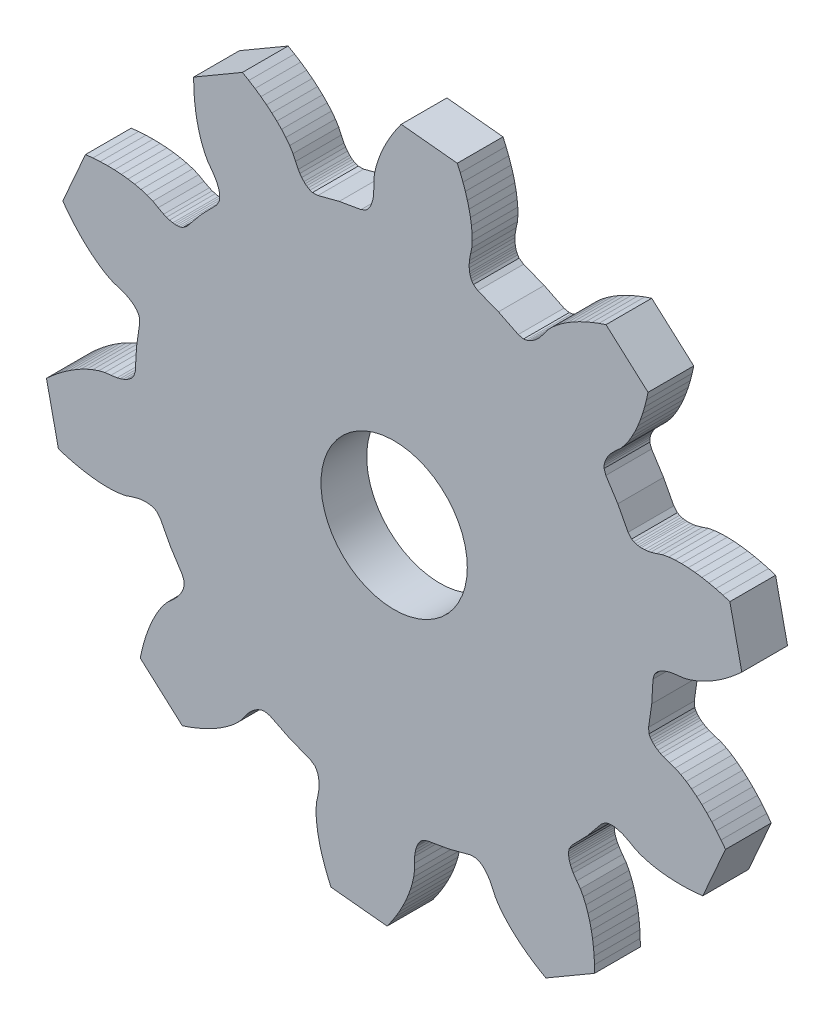
SolidWorks part; units mm, degrees
ref_plane "Front Plane" through (0, 0, 0) normal (0, 0, 1) x (1, 0, 0)
ref_plane "Top Plane" through (0, 0, 0) normal (0, 1, 0) x (1, 0, 0)
ref_plane "Right Plane" through (0, 0, 0) normal (1, 0, 0) x (0, 0, -1)
sketch "Sketch1" plane through (0, 0, 0) normal (0, 0, 1) x (1, 0, 0)
  line L0 (8.112, 16.6609) -> (7.8643, 16.9436)
  line L1 (7.8643, 16.9436) -> (7.7104, 17.0282)
  line L2 (7.7104, 17.0282) -> (7.5725, 17.0779)
  line L3 (7.5725, 17.0779) -> (7.4432, 17.1089)
  line L4 (7.4432, 17.1089) -> (7.3198, 17.1275)
  line L5 (7.3198, 17.1275) -> (7.2004, 17.1366)
  line L6 (7.2004, 17.1366) -> (6.971, 17.1338)
  line L7 (6.971, 17.1338) -> (6.7508, 17.1099)
  line L8 (6.7508, 17.1099) -> (6.5372, 17.0698)
  line L9 (6.5372, 17.0698) -> (6.1262, 16.9512)
  line L10 (6.1262, 16.9512) -> (5.7224, 16.8153)
  line L11 (5.7224, 16.8153) -> (5.2951, 16.7376)
  line L12 (5.2951, 16.7376) -> (4.8534, 16.6975)
  line L13 (4.8534, 16.6975) -> (4.4008, 16.6875)
  line L14 (4.4008, 16.6875) -> (3.9395, 16.7046)
  line L15 (3.9395, 16.7046) -> (3.4704, 16.7465)
  line L16 (3.4704, 16.7465) -> (2.9949, 16.812)
  line L17 (2.9949, 16.812) -> (2.5141, 16.9001)
  line L18 (2.5141, 16.9001) -> (2.0282, 17.0109)
  line L19 (2.0282, 17.0109) -> (1.5385, 17.1432)
  line L20 (1.5385, 17.1432) -> (1.0457, 17.2971)
  line L21 (1.0457, 17.2971) -> (0.2156, 21.1229)
  line L22 (0.2156, 21.1229) -> (0.6005, 21.4671)
  line L23 (0.6005, 21.4671) -> (0.9914, 21.7907)
  line L24 (0.9914, 21.7907) -> (1.3876, 22.0924)
  line L25 (1.3876, 22.0924) -> (1.7887, 22.3723)
  line L26 (1.7887, 22.3723) -> (2.1943, 22.6289)
  line L27 (2.1943, 22.6289) -> (2.6038, 22.8613)
  line L28 (2.6038, 22.8613) -> (3.0168, 23.068)
  line L29 (3.0168, 23.068) -> (3.4328, 23.2463)
  line L30 (3.4328, 23.2463) -> (3.8514, 23.3929)
  line L31 (3.8514, 23.3929) -> (4.2723, 23.4993)
  line L32 (4.2723, 23.4993) -> (4.6962, 23.543)
  line L33 (4.6962, 23.543) -> (5.1196, 23.6052)
  line L34 (5.1196, 23.6052) -> (5.3304, 23.6571)
  line L35 (5.3304, 23.6571) -> (5.5408, 23.7269)
  line L36 (5.5408, 23.7269) -> (5.7508, 23.8194)
  line L37 (5.7508, 23.8194) -> (5.8555, 23.8773)
  line L38 (5.8555, 23.8773) -> (5.9604, 23.9451)
  line L39 (5.9604, 23.9451) -> (6.065, 24.0269)
  line L40 (6.065, 24.0269) -> (6.1697, 24.1295)
  line L41 (6.1697, 24.1295) -> (6.2748, 24.2702)
  line L42 (6.2748, 24.2702) -> (6.383, 24.6301)
  line L43 (6.383, 24.6301) -> (6.4719, 26.1612)
  line L44 (6.4719, 26.1612) -> (6.6906, 27.6794)
  line L45 (6.6906, 27.6794) -> (6.6566, 28.0535)
  line L46 (6.6566, 28.0535) -> (6.5816, 28.2125)
  line L47 (6.5816, 28.2125) -> (6.4994, 28.334)
  line L48 (6.4994, 28.334) -> (6.4132, 28.435)
  line L49 (6.4132, 28.435) -> (6.3241, 28.5224)
  line L50 (6.3241, 28.5224) -> (6.2329, 28.5999)
  line L51 (6.2329, 28.5999) -> (6.0457, 28.7327)
  line L52 (6.0457, 28.7327) -> (5.8534, 28.843)
  line L53 (5.8534, 28.843) -> (5.6573, 28.9359)
  line L54 (5.6573, 28.9359) -> (5.255, 29.0815)
  line L55 (5.255, 29.0815) -> (4.8484, 29.209)
  line L56 (4.8484, 29.209) -> (4.4569, 29.3972)
  line L57 (4.4569, 29.3972) -> (4.0759, 29.6245)
  line L58 (4.0759, 29.6245) -> (3.7041, 29.8823)
  line L59 (3.7041, 29.8823) -> (3.3409, 30.1673)
  line L60 (3.3409, 30.1673) -> (2.986, 30.4767)
  line L61 (2.986, 30.4767) -> (2.6398, 30.8092)
  line L62 (2.6398, 30.8092) -> (2.3025, 31.1635)
  line L63 (2.3025, 31.1635) -> (1.9746, 31.5384)
  line L64 (1.9746, 31.5384) -> (1.6563, 31.9334)
  line L65 (1.6563, 31.9334) -> (1.348, 32.3477)
  line L66 (1.348, 32.3477) -> (2.9253, 35.9306)
  line L67 (2.9253, 35.9306) -> (3.4389, 35.9829)
  line L68 (3.4389, 35.9829) -> (3.9451, 36.0149)
  line L69 (3.9451, 36.0149) -> (4.4432, 36.0261)
  line L70 (4.4432, 36.0261) -> (4.9322, 36.0167)
  line L71 (4.9322, 36.0167) -> (5.4112, 35.986)
  line L72 (5.4112, 35.986) -> (5.8791, 35.9334)
  line L73 (5.8791, 35.9334) -> (6.3345, 35.8577)
  line L74 (6.3345, 35.8577) -> (6.776, 35.7576)
  line L75 (6.776, 35.7576) -> (7.2009, 35.6301)
  line L76 (7.2009, 35.6301) -> (7.604, 35.4688)
  line L77 (7.604, 35.4688) -> (7.9726, 35.2549)
  line L78 (7.9726, 35.2549) -> (8.3515, 35.0566)
  line L79 (8.3515, 35.0566) -> (8.5527, 34.9745)
  line L80 (8.5527, 34.9745) -> (8.7638, 34.9072)
  line L81 (8.7638, 34.9072) -> (8.988, 34.8587)
  line L82 (8.988, 34.8587) -> (9.1069, 34.844)
  line L83 (9.1069, 34.844) -> (9.2316, 34.8374)
  line L84 (9.2316, 34.8374) -> (9.3645, 34.8419)
  line L85 (9.3645, 34.8419) -> (9.5095, 34.8633)
  line L86 (9.5095, 34.8633) -> (9.6771, 34.9153)
  line L87 (9.6771, 34.9153) -> (9.9764, 35.1429)
  line L88 (9.9764, 35.1429) -> (10.9482, 36.3296)
  line L89 (10.9482, 36.3296) -> (12.0175, 37.4289)
  line L90 (12.0175, 37.4289) -> (12.2098, 37.7518)
  line L91 (12.2098, 37.7518) -> (12.2425, 37.9245)
  line L92 (12.2425, 37.9245) -> (12.2474, 38.071)
  line L93 (12.2474, 38.071) -> (12.237, 38.2034)
  line L94 (12.237, 38.2034) -> (12.2164, 38.3266)
  line L95 (12.2164, 38.3266) -> (12.1882, 38.4429)
  line L96 (12.1882, 38.4429) -> (12.1148, 38.6603)
  line L97 (12.1148, 38.6603) -> (12.0241, 38.8625)
  line L98 (12.0241, 38.8625) -> (11.92, 39.053)
  line L99 (11.92, 39.053) -> (11.6799, 39.4071)
  line L100 (11.6799, 39.4071) -> (11.4259, 39.7495)
  line L101 (11.4259, 39.7495) -> (11.2199, 40.1317)
  line L102 (11.2199, 40.1317) -> (11.0454, 40.5394)
  line L103 (11.0454, 40.5394) -> (10.8961, 40.9666)
  line L104 (10.8961, 40.9666) -> (10.7696, 41.4109)
  line L105 (10.7696, 41.4109) -> (10.6644, 41.8699)
  line L106 (10.6644, 41.8699) -> (10.5799, 42.3423)
  line L107 (10.5799, 42.3423) -> (10.5153, 42.8269)
  line L108 (10.5153, 42.8269) -> (10.4704, 43.3233)
  line L109 (10.4704, 43.3233) -> (10.445, 43.8297)
  line L110 (10.445, 43.8297) -> (10.4389, 44.3461)
  line L111 (10.4389, 44.3461) -> (13.8212, 46.3177)
  line L112 (13.8212, 46.3177) -> (14.2674, 46.0581)
  line L113 (14.2674, 46.0581) -> (14.6957, 45.7863)
  line L114 (14.6957, 45.7863) -> (15.1054, 45.5028)
  line L115 (15.1054, 45.5028) -> (15.4953, 45.2077)
  line L116 (15.4953, 45.2077) -> (15.8648, 44.9014)
  line L117 (15.8648, 44.9014) -> (16.2123, 44.5836)
  line L118 (16.2123, 44.5836) -> (16.5364, 44.2547)
  line L119 (16.5364, 44.2547) -> (16.8349, 43.9143)
  line L120 (16.8349, 43.9143) -> (17.1033, 43.5615)
  line L121 (17.1033, 43.5615) -> (17.3347, 43.194)
  line L122 (17.3347, 43.194) -> (17.5072, 42.8043)
  line L123 (17.5072, 42.8043) -> (17.6972, 42.421)
  line L124 (17.6972, 42.421) -> (17.8117, 42.2364)
  line L125 (17.8117, 42.2364) -> (17.9431, 42.0578)
  line L126 (17.9431, 42.0578) -> (18.096, 41.8869)
  line L127 (18.096, 41.8869) -> (18.1834, 41.8051)
  line L128 (18.1834, 41.8051) -> (18.2804, 41.7264)
  line L129 (18.2804, 41.7264) -> (18.3906, 41.6522)
  line L130 (18.3906, 41.6522) -> (18.5204, 41.5841)
  line L131 (18.5204, 41.5841) -> (18.6868, 41.5275)
  line L132 (18.6868, 41.5275) -> (19.0624, 41.5359)
  line L133 (19.0624, 41.5359) -> (20.5461, 41.9247)
  line L134 (20.5461, 41.9247) -> (22.0576, 42.1856)
  line L135 (22.0576, 42.1856) -> (22.4031, 42.3337)
  line L136 (22.4031, 42.3337) -> (22.5308, 42.4541)
  line L137 (22.5308, 42.4541) -> (22.621, 42.5699)
  line L138 (22.621, 42.5699) -> (22.6903, 42.6832)
  line L139 (22.6903, 42.6832) -> (22.7462, 42.7949)
  line L140 (22.7462, 42.7949) -> (22.7917, 42.9054)
  line L141 (22.7917, 42.9054) -> (22.86, 43.1246)
  line L142 (22.86, 43.1246) -> (22.9055, 43.3413)
  line L143 (22.9055, 43.3413) -> (22.9332, 43.5569)
  line L144 (22.9332, 43.5569) -> (22.9474, 43.9844)
  line L145 (22.9474, 43.9844) -> (22.9428, 44.4106)
  line L146 (22.9428, 44.4106) -> (23.001, 44.8409)
  line L147 (23.001, 44.8409) -> (23.0995, 45.2735)
  line L148 (23.0995, 45.2735) -> (23.2298, 45.7068)
  line L149 (23.2298, 45.7068) -> (23.3886, 46.1404)
  line L150 (23.3886, 46.1404) -> (23.5732, 46.5734)
  line L151 (23.5732, 46.5734) -> (23.7825, 47.0055)
  line L152 (23.7825, 47.0055) -> (24.0152, 47.4358)
  line L153 (24.0152, 47.4358) -> (24.2705, 47.8635)
  line L154 (24.2705, 47.8635) -> (24.5476, 48.2882)
  line L155 (24.5476, 48.2882) -> (24.8463, 48.7096)
  line L156 (24.8463, 48.7096) -> (28.7414, 48.3166)
  line L157 (28.7414, 48.3166) -> (28.9499, 47.8442)
  line L158 (28.9499, 47.8442) -> (29.1366, 47.3725)
  line L159 (29.1366, 47.3725) -> (29.3014, 46.9024)
  line L160 (29.3014, 46.9024) -> (29.4434, 46.4345)
  line L161 (29.4434, 46.4345) -> (29.5623, 45.9694)
  line L162 (29.5623, 45.9694) -> (29.6568, 45.5082)
  line L163 (29.6568, 45.5082) -> (29.7256, 45.0515)
  line L164 (29.7256, 45.0515) -> (29.7668, 44.6009)
  line L165 (29.7668, 44.6009) -> (29.7767, 44.1574)
  line L166 (29.7767, 44.1574) -> (29.748, 43.7241)
  line L167 (29.748, 43.7241) -> (29.6583, 43.3075)
  line L168 (29.6583, 43.3075) -> (29.5869, 42.8856)
  line L169 (29.5869, 42.8856) -> (29.5709, 42.669)
  line L170 (29.5709, 42.669) -> (29.5722, 42.4475)
  line L171 (29.5722, 42.4475) -> (29.5956, 42.2191)
  line L172 (29.5956, 42.2191) -> (29.6179, 42.1018)
  line L173 (29.6179, 42.1018) -> (29.6504, 41.9811)
  line L174 (29.6504, 41.9811) -> (29.6956, 41.8562)
  line L175 (29.6956, 41.8562) -> (29.7609, 41.7248)
  line L176 (29.7609, 41.7248) -> (29.8623, 41.5813)
  line L177 (29.8623, 41.5813) -> (30.1709, 41.3672)
  line L178 (30.1709, 41.3672) -> (31.5999, 40.8097)
  line L179 (31.5999, 40.8097) -> (32.9761, 40.1325)
  line L180 (32.9761, 40.1325) -> (33.3426, 40.0492)
  line L181 (33.3426, 40.0492) -> (33.5168, 40.0713)
  line L182 (33.5168, 40.0713) -> (33.6575, 40.1122)
  line L183 (33.6575, 40.1122) -> (33.7805, 40.163)
  line L184 (33.7805, 40.163) -> (33.8912, 40.2206)
  line L185 (33.8912, 40.2206) -> (33.9931, 40.2834)
  line L186 (33.9931, 40.2834) -> (34.177, 40.4203)
  line L187 (34.177, 40.4203) -> (34.3413, 40.5691)
  line L188 (34.3413, 40.5691) -> (34.4904, 40.7271)
  line L189 (34.4904, 40.7271) -> (34.753, 41.0647)
  line L190 (34.753, 41.0647) -> (34.9999, 41.4119)
  line L191 (34.9999, 41.4119) -> (35.3002, 41.7261)
  line L192 (35.3002, 41.7261) -> (35.6339, 42.0179)
  line L193 (35.6339, 42.0179) -> (35.9941, 42.292)
  line L194 (35.9941, 42.292) -> (36.3774, 42.5496)
  line L195 (36.3774, 42.5496) -> (36.7815, 42.7914)
  line L196 (36.7815, 42.7914) -> (37.2047, 43.0179)
  line L197 (37.2047, 43.0179) -> (37.6456, 43.229)
  line L198 (37.6456, 43.229) -> (38.1036, 43.4251)
  line L199 (38.1036, 43.4251) -> (38.5775, 43.606)
  line L200 (38.5775, 43.606) -> (39.0667, 43.7711)
  line L201 (39.0667, 43.7711) -> (41.987, 41.1637)
  line L202 (41.987, 41.1637) -> (41.878, 40.659)
  line L203 (41.878, 40.659) -> (41.752, 40.1678)
  line L204 (41.752, 40.1678) -> (41.6088, 39.6905)
  line L205 (41.6088, 39.6905) -> (41.4487, 39.2285)
  line L206 (41.4487, 39.2285) -> (41.2714, 38.7825)
  line L207 (41.2714, 38.7825) -> (41.0769, 38.3537)
  line L208 (41.0769, 38.3537) -> (40.8643, 37.9438)
  line L209 (40.8643, 37.9438) -> (40.6326, 37.5549)
  line L210 (40.6326, 37.5549) -> (40.3802, 37.1904)
  line L211 (40.3802, 37.1904) -> (40.102, 36.8567)
  line L212 (40.102, 36.8567) -> (39.7845, 36.5722)
  line L213 (39.7845, 36.5722) -> (39.4787, 36.2732)
  line L214 (39.4787, 36.2732) -> (39.3388, 36.1071)
  line L215 (39.3388, 36.1071) -> (39.2095, 35.9273)
  line L216 (39.2095, 35.9273) -> (39.0942, 35.7289)
  line L217 (39.0942, 35.7289) -> (39.0431, 35.6205)
  line L218 (39.0431, 35.6205) -> (38.9984, 35.5039)
  line L219 (38.9984, 35.5039) -> (38.9618, 35.3764)
  line L220 (38.9618, 35.3764) -> (38.9372, 35.2318)
  line L221 (38.9372, 35.2318) -> (38.9349, 35.0561)
  line L222 (38.9349, 35.0561) -> (39.0588, 34.7012)
  line L223 (39.0588, 34.7012) -> (39.8871, 33.4104)
  line L224 (39.8871, 33.4104) -> (40.6024, 32.0535)
  line L225 (40.6024, 32.0535) -> (40.8501, 31.7708)
  line L226 (40.8501, 31.7708) -> (41.004, 31.6862)
  line L227 (41.004, 31.6862) -> (41.1419, 31.6365)
  line L228 (41.1419, 31.6365) -> (41.2712, 31.6055)
  line L229 (41.2712, 31.6055) -> (41.3946, 31.5869)
  line L230 (41.3946, 31.5869) -> (41.5138, 31.5778)
  line L231 (41.5138, 31.5778) -> (41.7434, 31.5806)
  line L232 (41.7434, 31.5806) -> (41.9636, 31.6045)
  line L233 (41.9636, 31.6045) -> (42.1772, 31.6446)
  line L234 (42.1772, 31.6446) -> (42.5882, 31.7632)
  line L235 (42.5882, 31.7632) -> (42.992, 31.8991)
  line L236 (42.992, 31.8991) -> (43.4193, 31.9768)
  line L237 (43.4193, 31.9768) -> (43.861, 32.017)
  line L238 (43.861, 32.017) -> (44.3136, 32.0269)
  line L239 (44.3136, 32.0269) -> (44.7749, 32.0098)
  line L240 (44.7749, 32.0098) -> (45.244, 31.9679)
  line L241 (45.244, 31.9679) -> (45.7195, 31.9024)
  line L242 (45.7195, 31.9024) -> (46.2003, 31.814)
  line L243 (46.2003, 31.814) -> (46.6862, 31.7035)
  line L244 (46.6862, 31.7035) -> (47.1759, 31.5712)
  line L245 (47.1759, 31.5712) -> (47.6687, 31.4173)
  line L246 (47.6687, 31.4173) -> (48.4988, 27.5915)
  line L247 (48.4988, 27.5915) -> (48.1139, 27.2473)
  line L248 (48.1139, 27.2473) -> (47.723, 26.9237)
  line L249 (47.723, 26.9237) -> (47.3268, 26.622)
  line L250 (47.3268, 26.622) -> (46.9257, 26.3421)
  line L251 (46.9257, 26.3421) -> (46.5201, 26.0855)
  line L252 (46.5201, 26.0855) -> (46.1107, 25.8531)
  line L253 (46.1107, 25.8531) -> (45.6976, 25.6464)
  line L254 (45.6976, 25.6464) -> (45.2816, 25.4681)
  line L255 (45.2816, 25.4681) -> (44.863, 25.3215)
  line L256 (44.863, 25.3215) -> (44.4421, 25.2151)
  line L257 (44.4421, 25.2151) -> (44.0182, 25.1714)
  line L258 (44.0182, 25.1714) -> (43.5948, 25.1092)
  line L259 (43.5948, 25.1092) -> (43.384, 25.0571)
  line L260 (43.384, 25.0571) -> (43.1737, 24.9875)
  line L261 (43.1737, 24.9875) -> (42.9636, 24.895)
  line L262 (42.9636, 24.895) -> (42.8589, 24.8371)
  line L263 (42.8589, 24.8371) -> (42.754, 24.7693)
  line L264 (42.754, 24.7693) -> (42.6494, 24.6875)
  line L265 (42.6494, 24.6875) -> (42.5445, 24.5849)
  line L266 (42.5445, 24.5849) -> (42.4396, 24.4442)
  line L267 (42.4396, 24.4442) -> (42.3314, 24.0843)
  line L268 (42.3314, 24.0843) -> (42.2425, 22.5532)
  line L269 (42.2425, 22.5532) -> (42.0238, 21.035)
  line L270 (42.0238, 21.035) -> (42.0578, 20.6606)
  line L271 (42.0578, 20.6606) -> (42.1328, 20.5019)
  line L272 (42.1328, 20.5019) -> (42.2151, 20.3805)
  line L273 (42.2151, 20.3805) -> (42.3012, 20.2794)
  line L274 (42.3012, 20.2794) -> (42.3903, 20.192)
  line L275 (42.3903, 20.192) -> (42.4815, 20.1145)
  line L276 (42.4815, 20.1145) -> (42.6687, 19.9817)
  line L277 (42.6687, 19.9817) -> (42.861, 19.8714)
  line L278 (42.861, 19.8714) -> (43.0571, 19.7785)
  line L279 (43.0571, 19.7785) -> (43.4594, 19.6329)
  line L280 (43.4594, 19.6329) -> (43.8661, 19.5054)
  line L281 (43.8661, 19.5054) -> (44.2575, 19.3172)
  line L282 (44.2575, 19.3172) -> (44.6385, 19.0899)
  line L283 (44.6385, 19.0899) -> (45.0103, 18.8321)
  line L284 (45.0103, 18.8321) -> (45.3735, 18.5471)
  line L285 (45.3735, 18.5471) -> (45.7284, 18.2375)
  line L286 (45.7284, 18.2375) -> (46.0746, 17.905)
  line L287 (46.0746, 17.905) -> (46.4119, 17.5509)
  line L288 (46.4119, 17.5509) -> (46.7398, 17.176)
  line L289 (46.7398, 17.176) -> (47.0581, 16.781)
  line L290 (47.0581, 16.781) -> (47.3664, 16.3667)
  line L291 (47.3664, 16.3667) -> (45.7891, 12.7838)
  line L292 (45.7891, 12.7838) -> (45.2755, 12.7315)
  line L293 (45.2755, 12.7315) -> (44.7693, 12.6995)
  line L294 (44.7693, 12.6995) -> (44.2712, 12.6881)
  line L295 (44.2712, 12.6881) -> (43.7822, 12.6977)
  line L296 (43.7822, 12.6977) -> (43.3032, 12.7284)
  line L297 (43.3032, 12.7284) -> (42.8353, 12.781)
  line L298 (42.8353, 12.781) -> (42.3799, 12.8567)
  line L299 (42.3799, 12.8567) -> (41.9384, 12.9568)
  line L300 (41.9384, 12.9568) -> (41.5135, 13.0843)
  line L301 (41.5135, 13.0843) -> (41.1104, 13.2456)
  line L302 (41.1104, 13.2456) -> (40.7419, 13.4595)
  line L303 (40.7419, 13.4595) -> (40.3629, 13.6578)
  line L304 (40.3629, 13.6578) -> (40.1617, 13.7399)
  line L305 (40.1617, 13.7399) -> (39.9504, 13.8072)
  line L306 (39.9504, 13.8072) -> (39.7261, 13.8557)
  line L307 (39.7261, 13.8557) -> (39.6075, 13.8704)
  line L308 (39.6075, 13.8704) -> (39.4828, 13.877)
  line L309 (39.4828, 13.877) -> (39.3499, 13.8725)
  line L310 (39.3499, 13.8725) -> (39.2049, 13.8511)
  line L311 (39.2049, 13.8511) -> (39.0373, 13.7991)
  line L312 (39.0373, 13.7991) -> (38.738, 13.5715)
  line L313 (38.738, 13.5715) -> (37.7662, 12.3848)
  line L314 (37.7662, 12.3848) -> (36.6969, 11.2855)
  line L315 (36.6969, 11.2855) -> (36.5046, 10.9626)
  line L316 (36.5046, 10.9626) -> (36.4719, 10.7899)
  line L317 (36.4719, 10.7899) -> (36.467, 10.6434)
  line L318 (36.467, 10.6434) -> (36.4774, 10.511)
  line L319 (36.4774, 10.511) -> (36.498, 10.3878)
  line L320 (36.498, 10.3878) -> (36.5262, 10.2715)
  line L321 (36.5262, 10.2715) -> (36.5996, 10.0541)
  line L322 (36.5996, 10.0541) -> (36.6903, 9.8519)
  line L323 (36.6903, 9.8519) -> (36.7944, 9.6614)
  line L324 (36.7944, 9.6614) -> (37.0345, 9.3071)
  line L325 (37.0345, 9.3071) -> (37.2885, 8.9649)
  line L326 (37.2885, 8.9649) -> (37.4945, 8.5827)
  line L327 (37.4945, 8.5827) -> (37.669, 8.175)
  line L328 (37.669, 8.175) -> (37.8183, 7.7478)
  line L329 (37.8183, 7.7478) -> (37.9448, 7.3035)
  line L330 (37.9448, 7.3035) -> (38.05, 6.8445)
  line L331 (38.05, 6.8445) -> (38.1345, 6.3721)
  line L332 (38.1345, 6.3721) -> (38.1991, 5.8875)
  line L333 (38.1991, 5.8875) -> (38.244, 5.3911)
  line L334 (38.244, 5.3911) -> (38.2694, 4.8847)
  line L335 (38.2694, 4.8847) -> (38.2755, 4.3683)
  line L336 (38.2755, 4.3683) -> (34.8933, 2.3967)
  line L337 (34.8933, 2.3967) -> (34.447, 2.6563)
  line L338 (34.447, 2.6563) -> (34.0187, 2.9281)
  line L339 (34.0187, 2.9281) -> (33.609, 3.2116)
  line L340 (33.609, 3.2116) -> (33.2191, 3.5067)
  line L341 (33.2191, 3.5067) -> (32.8496, 3.813)
  line L342 (32.8496, 3.813) -> (32.5021, 4.1308)
  line L343 (32.5021, 4.1308) -> (32.178, 4.4597)
  line L344 (32.178, 4.4597) -> (31.8795, 4.8001)
  line L345 (31.8795, 4.8001) -> (31.6108, 5.1529)
  line L346 (31.6108, 5.1529) -> (31.3797, 5.5204)
  line L347 (31.3797, 5.5204) -> (31.2069, 5.9101)
  line L348 (31.2069, 5.9101) -> (31.0172, 6.2934)
  line L349 (31.0172, 6.2934) -> (30.9027, 6.478)
  line L350 (30.9027, 6.478) -> (30.7713, 6.6566)
  line L351 (30.7713, 6.6566) -> (30.6184, 6.8275)
  line L352 (30.6184, 6.8275) -> (30.5311, 6.9093)
  line L353 (30.5311, 6.9093) -> (30.434, 6.988)
  line L354 (30.434, 6.988) -> (30.3238, 7.0622)
  line L355 (30.3238, 7.0622) -> (30.194, 7.1303)
  line L356 (30.194, 7.1303) -> (30.0276, 7.1869)
  line L357 (30.0276, 7.1869) -> (29.652, 7.1785)
  line L358 (29.652, 7.1785) -> (28.1683, 6.7897)
  line L359 (28.1683, 6.7897) -> (26.6568, 6.5288)
  line L360 (26.6568, 6.5288) -> (26.3114, 6.3807)
  line L361 (26.3114, 6.3807) -> (26.1836, 6.2603)
  line L362 (26.1836, 6.2603) -> (26.0934, 6.1445)
  line L363 (26.0934, 6.1445) -> (26.0241, 6.0312)
  line L364 (26.0241, 6.0312) -> (25.9682, 5.9195)
  line L365 (25.9682, 5.9195) -> (25.9227, 5.809)
  line L366 (25.9227, 5.809) -> (25.8544, 5.5898)
  line L367 (25.8544, 5.5898) -> (25.8089, 5.3729)
  line L368 (25.8089, 5.3729) -> (25.7813, 5.1575)
  line L369 (25.7813, 5.1575) -> (25.767, 4.73)
  line L370 (25.767, 4.73) -> (25.7716, 4.3038)
  line L371 (25.7716, 4.3038) -> (25.7134, 3.8735)
  line L372 (25.7134, 3.8735) -> (25.6149, 3.4409)
  line L373 (25.6149, 3.4409) -> (25.4846, 3.0076)
  line L374 (25.4846, 3.0076) -> (25.3258, 2.574)
  line L375 (25.3258, 2.574) -> (25.1412, 2.141)
  line L376 (25.1412, 2.141) -> (24.9319, 1.7089)
  line L377 (24.9319, 1.7089) -> (24.6992, 1.2786)
  line L378 (24.6992, 1.2786) -> (24.4439, 0.8509)
  line L379 (24.4439, 0.8509) -> (24.1668, 0.4262)
  line L380 (24.1668, 0.4262) -> (23.8681, 0.0048)
  line L381 (23.8681, 0.0048) -> (19.973, 0.3978)
  line L382 (19.973, 0.3978) -> (19.7645, 0.8702)
  line L383 (19.7645, 0.8702) -> (19.5778, 1.3419)
  line L384 (19.5778, 1.3419) -> (19.413, 1.812)
  line L385 (19.413, 1.812) -> (19.271, 2.2799)
  line L386 (19.271, 2.2799) -> (19.1521, 2.745)
  line L387 (19.1521, 2.745) -> (19.0576, 3.2062)
  line L388 (19.0576, 3.2062) -> (18.9888, 3.6629)
  line L389 (18.9888, 3.6629) -> (18.9476, 4.1135)
  line L390 (18.9476, 4.1135) -> (18.9375, 4.557)
  line L391 (18.9375, 4.557) -> (18.9664, 4.9903)
  line L392 (18.9664, 4.9903) -> (19.0558, 5.4069)
  line L393 (19.0558, 5.4069) -> (19.1275, 5.8288)
  line L394 (19.1275, 5.8288) -> (19.1435, 6.0455)
  line L395 (19.1435, 6.0455) -> (19.1422, 6.2669)
  line L396 (19.1422, 6.2669) -> (19.1188, 6.4953)
  line L397 (19.1188, 6.4953) -> (19.0965, 6.6126)
  line L398 (19.0965, 6.6126) -> (19.064, 6.7333)
  line L399 (19.064, 6.7333) -> (19.0188, 6.8583)
  line L400 (19.0188, 6.8583) -> (18.9535, 6.9896)
  line L401 (18.9535, 6.9896) -> (18.8521, 7.1331)
  line L402 (18.8521, 7.1331) -> (18.5433, 7.3472)
  line L403 (18.5433, 7.3472) -> (17.1145, 7.9047)
  line L404 (17.1145, 7.9047) -> (15.7383, 8.5819)
  line L405 (15.7383, 8.5819) -> (15.3718, 8.6652)
  line L406 (15.3718, 8.6652) -> (15.1976, 8.6431)
  line L407 (15.1976, 8.6431) -> (15.0569, 8.6022)
  line L408 (15.0569, 8.6022) -> (14.9339, 8.5514)
  line L409 (14.9339, 8.5514) -> (14.8232, 8.4938)
  line L410 (14.8232, 8.4938) -> (14.7213, 8.431)
  line L411 (14.7213, 8.431) -> (14.5372, 8.2941)
  line L412 (14.5372, 8.2941) -> (14.3731, 8.1453)
  line L413 (14.3731, 8.1453) -> (14.224, 7.9873)
  line L414 (14.224, 7.9873) -> (13.9614, 7.6497)
  line L415 (13.9614, 7.6497) -> (13.7145, 7.3022)
  line L416 (13.7145, 7.3022) -> (13.4142, 6.9883)
  line L417 (13.4142, 6.9883) -> (13.0805, 6.6965)
  line L418 (13.0805, 6.6965) -> (12.7203, 6.4224)
  line L419 (12.7203, 6.4224) -> (12.337, 6.1648)
  line L420 (12.337, 6.1648) -> (11.9329, 5.923)
  line L421 (11.9329, 5.923) -> (11.5098, 5.6965)
  line L422 (11.5098, 5.6965) -> (11.0688, 5.4854)
  line L423 (11.0688, 5.4854) -> (10.6108, 5.2893)
  line L424 (10.6108, 5.2893) -> (10.1369, 5.1084)
  line L425 (10.1369, 5.1084) -> (9.6477, 4.9433)
  line L426 (9.6477, 4.9433) -> (6.7274, 7.5507)
  line L427 (6.7274, 7.5507) -> (6.8364, 8.0554)
  line L428 (6.8364, 8.0554) -> (6.9624, 8.5466)
  line L429 (6.9624, 8.5466) -> (7.1056, 9.0239)
  line L430 (7.1056, 9.0239) -> (7.2657, 9.4859)
  line L431 (7.2657, 9.4859) -> (7.443, 9.9319)
  line L432 (7.443, 9.9319) -> (7.6375, 10.3607)
  line L433 (7.6375, 10.3607) -> (7.8501, 10.7706)
  line L434 (7.8501, 10.7706) -> (8.0818, 11.1595)
  line L435 (8.0818, 11.1595) -> (8.3342, 11.524)
  line L436 (8.3342, 11.524) -> (8.6124, 11.8577)
  line L437 (8.6124, 11.8577) -> (8.9296, 12.1422)
  line L438 (8.9296, 12.1422) -> (9.2357, 12.4412)
  line L439 (9.2357, 12.4412) -> (9.3756, 12.6073)
  line L440 (9.3756, 12.6073) -> (9.5049, 12.7871)
  line L441 (9.5049, 12.7871) -> (9.6202, 12.9855)
  line L442 (9.6202, 12.9855) -> (9.671, 13.094)
  line L443 (9.671, 13.094) -> (9.716, 13.2105)
  line L444 (9.716, 13.2105) -> (9.7526, 13.338)
  line L445 (9.7526, 13.338) -> (9.7772, 13.4826)
  line L446 (9.7772, 13.4826) -> (9.7795, 13.6583)
  line L447 (9.7795, 13.6583) -> (9.6556, 14.0132)
  line L448 (9.6556, 14.0132) -> (8.8273, 15.304)
  line L449 (8.8273, 15.304) -> (8.112, 16.6609)
  circle A0 centre (24.3571, 24.3571) radius 5.08
extrude "Boss-Extrude1" add sketch "Sketch1" along normal blind 3.175
